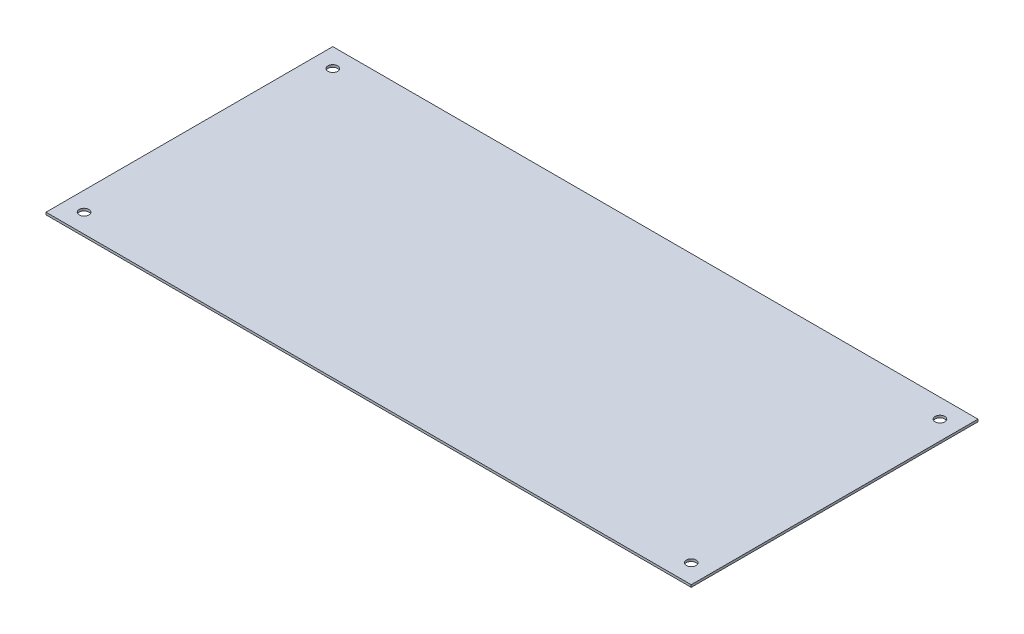
SolidWorks part; units mm, degrees
ref_plane "Front Plane" through (0, 0, 0) normal (0, 0, 1) x (1, 0, 0)
ref_plane "Top Plane" through (0, 0, 0) normal (0, 1, 0) x (1, 0, 0)
ref_plane "Right Plane" through (0, 0, 0) normal (1, 0, 0) x (0, 0, -1)
sketch "Sketch2" plane through (0, 0, 0) normal (0, 1, 0) x (1, 0, 0)
  line L1 (-223, 96) -> (218, 96)
  line L2 (-223, 96) -> (-223, -100)
  line L3 (-223, -100) -> (218, -100)
  line L4 (218, 96) -> (218, -100)
extrude "Boss-Extrude1" add sketch "Sketch2" along normal blind 1.6
sketch "Sketch5" plane through (0, 1.6, 0) normal (0, 1, 0) x (1, 0, 0)
  line L0 (-2.5, 96) -> (-2.5, -100) construction
  line L1 (-223, -2) -> (218, -2) construction
  line L5 (-223, 96) -> (-223, -100) construction
  line L6 (218, -100) -> (218, 96) construction
  line L7 (218, 96) -> (-223, 96) construction
  line L8 (-223, -100) -> (218, -100) construction
  circle A0 centre (-210, 83) radius 3.3
  circle A4 centre (205, 83) radius 3.3
  circle A5 centre (205, -87) radius 3.3
  circle A6 centre (-210, -87) radius 3.3
extrude "Cut-Extrude1" cut sketch "Sketch5" against normal blind 1.6
